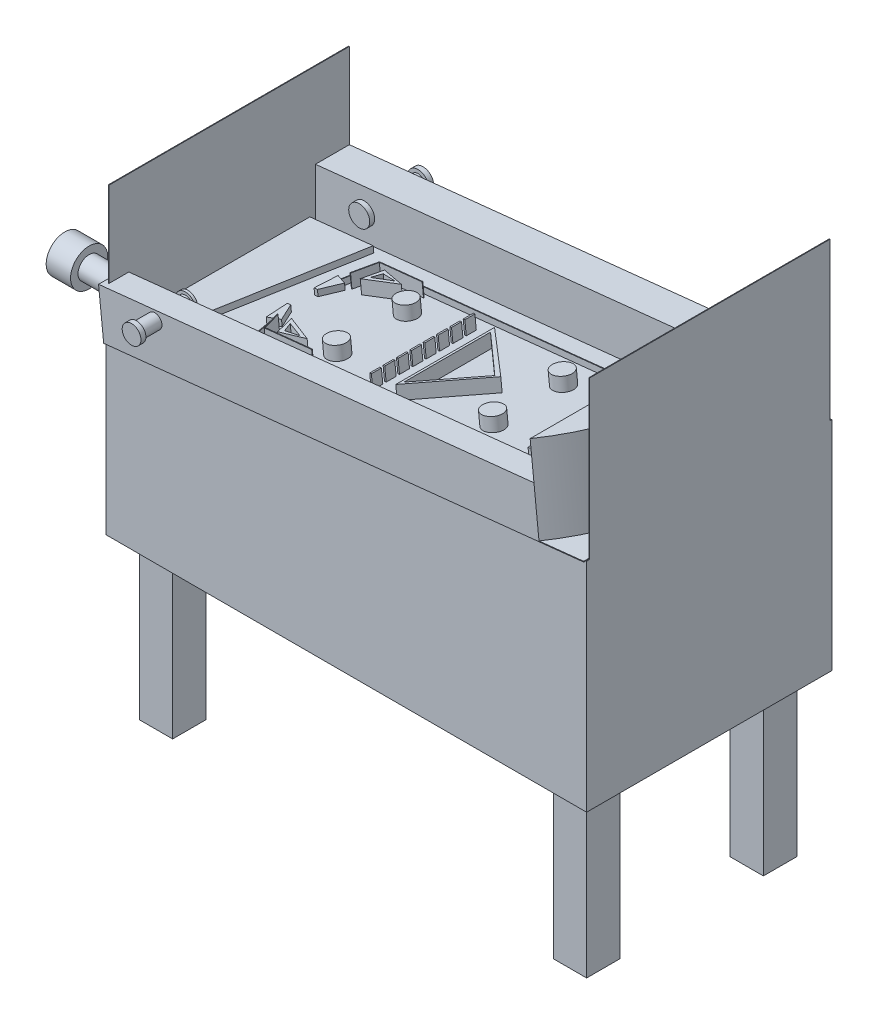
SolidWorks part; units mm, degrees
ref_plane "Front Plane" through (0, 0, 0) normal (0, 0, 1) x (1, 0, 0)
ref_plane "Top Plane" through (0, 0, 0) normal (0, 1, 0) x (1, 0, 0)
ref_plane "Right Plane" through (0, 0, 0) normal (1, 0, 0) x (0, 0, -1)
sketch "Sketch1" plane through (0, 0, 0) normal (0, 1, 0) x (1, 0, 0)
  line L1 (914.4, -457.2) -> (-914.4, -457.2)
  line L2 (914.4, -457.2) -> (914.4, 457.2)
  line L3 (914.4, 457.2) -> (-914.4, 457.2)
  line L4 (-914.4, -457.2) -> (-914.4, 457.2)
  line L5 (914.4, -457.2) -> (-914.4, 457.2) construction
  line L6 (914.4, 457.2) -> (-914.4, -457.2) construction
  point P0 (0, 0)
  dimension "D1" = 914.4
  dimension "D2" = 1828.8
extrude "Boss-Extrude1" add sketch "Sketch1" along normal blind 2.54
sketch "Sketch2" plane through (0, 2.54, 0) normal (0, 1, 0) x (1, 0, 0)
  line L0 (-914.4, 457.2) -> (-914.4, -457.2)
  line L1 (914.4, 457.2) -> (-914.4, 457.2) construction
  line L2 (-914.4, 457.2) -> (-914.4, -457.2) construction
  line L3 (-914.4, -457.2) -> (914.4, -457.2) construction
sketch "Sketch3" plane through (0, 2.54, 0) normal (0, 1, 0) x (1, 0, 0)
  line L0 (914.4, 457.2) -> (914.4, -457.2)
  line L1 (914.4, 457.2) -> (-914.4, 457.2) construction
  line L2 (914.4, -457.2) -> (914.4, 457.2) construction
extrude "Extrude-Thin8" add sketch "Sketch2" along normal blind 1143 separate body thin
extrude "Extrude-Thin9" add sketch "Sketch3" along normal blind 1422.4 thin
sketch "Sketch15" plane through (-914.4, 0, 0) normal (1, 0, 0) x (0, 0, -1)
  line L0 (-457.2, 1145.54) -> (457.2, 1145.54)
  line L1 (457.2, 1145.54) -> (-457.2, 1145.54) construction
  line L2 (457.2, 1145.54) -> (457.2, 2.54) construction
  line L3 (-457.2, 637.54) -> (457.2, 637.54) construction
  line L4 (-457.2, 1145.54) -> (-457.2, 2.54) construction
  line L5 (457.2, 2.54) -> (-457.2, 2.54) construction
  point P11 (0, 637.54)
  point P14 (0, 2.54)
  dimension "D1" = 635
sketch "Sketch17" plane through (911.86, 0, 0) normal (-1, 0, 0) x (0, 0, 1)
  line L0 (-457.2, 1424.94) -> (457.2, 1424.94)
  line L1 (-457.2, 829.7545) -> (477.8068, 829.7545) construction
  line L2 (-457.2, 1424.94) -> (-457.2, 2.54) construction
  line L3 (-457.2, 2.54) -> (457.2, 2.54) construction
  dimension "D1" = 827.2145
ref_plane "Plane3" through (-76.3845, 725.7414, 0) normal (0.1047, -0.9945, 0) x (-0.9945, -0.1047, 0)
sketch "Sketch18" plane through (-76.3845, 725.7414, 0) normal (0.1047, -0.9945, 0) x (-0.9945, -0.1047, 0)
  line L1 (842.6443, 457.2) -> (-993.7032, 457.2)
  line L2 (842.6443, 457.2) -> (842.6443, -477.8068)
  line L3 (842.6443, -477.8068) -> (-993.7032, -477.8068)
  line L4 (-993.7032, 457.2) -> (-993.7032, -477.8068)
extrude "Boss-Extrude3" add sketch "Sketch18" along normal blind 2.54
ref_plane "Plane4" through (-192.1612, 1256.0355, 0) normal (0.1512, -0.9885, 0) x (-0.9885, -0.1512, 0)
sketch "Sketch20" plane through (-76.3845, 725.7414, 0) normal (-0.1047, 0.9945, 0) x (0.9945, 0.1047, 0)
  line L0 (993.7032, 457.2) -> (-842.6443, 457.2)
sketch "Sketch22" plane through (911.86, 0, 0) normal (-1, 0, 0) x (0, 0, 1)
  line L0 (-457.2, 1424.94) -> (-457.2, 829.7545)
sketch "Sketch23" plane through (-914.4, 0, 0) normal (1, 0, 0) x (0, 0, -1)
  line L0 (457.2, 1145.54) -> (457.2, 637.54)
ref_plane "Plane5" through (0, 0, -457.2) normal (0, 0, -1) x (-1, 0, 0)
sketch "Sketch24" plane through (0, 0, -457.2) normal (0, 0, -1) x (-1, 0, 0)
  line L0 (916.94, 1145.54) -> (914.4, 637.54)
  line L1 (914.4, 637.54) -> (-911.86, 827.2005)
  line L2 (-911.86, 827.2005) -> (-911.86, 1424.94)
  line L3 (-911.86, 1424.94) -> (916.94, 1145.54)
sketch "Sketch25" plane through (0, 0, -457.2) normal (0, 0, -1) x (-1, 0, 0)
  line L0 (-914.4, 0) -> (914.4, 0)
  line L1 (914.4, 0) -> (914.1341, 635.014)
sketch "Sketch26" plane through (0, 0, 0) normal (0, 0, 1) x (1, 0, 0)
  line L1 (911.86, 829.7545) -> (-914.4, 637.54) construction
  line L2 (914.4, 0) -> (-914.4, 0) construction
  line L3 (914.4, 0) -> (-914.4, 0)
  line L4 (-914.4, 0) -> (-914.4, 637.54)
  line L5 (-916.94, 1145.54) -> (-914.4, 637.54) construction
  line L7 (-914.4, 637.54) -> (914.4, 827.2145)
  line L8 (914.4, 827.2145) -> (914.4, 0)
  dimension "D1" = 914.4
  dimension "D2" = 827.2145
  dimension "D3" = 1828.8
extrude "Boss-Extrude8" add sketch "Sketch26" along normal blind 469.138 and the other way blind 463.804
sketch "Sketch29" plane through (0, 0, 0) normal (0, -1, 0) x (1, 0, 0)
  line L0 (-787.4, 469.138) -> (-787.4, -457.4404) construction
  line L1 (-914.4, 469.138) -> (914.4, 469.138) construction
  line L3 (787.5718, 469.138) -> (787.5718, -457.2) construction
  line L4 (914.4, -457.2) -> (-914.4, -457.2) construction
  line L5 (-914.4, -330.2) -> (787.5718, -330.2) construction
  line L6 (-914.4, -463.804) -> (-914.4, 469.138) construction
  line L7 (-914.4, 342.138) -> (787.5718, 342.138) construction
  line L9 (-723.9, 278.638) -> (-850.9, 278.638)
  line L10 (-723.9, 278.638) -> (-723.9, 405.638)
  line L11 (-723.9, 405.638) -> (-850.9, 405.638)
  line L12 (-850.9, 278.638) -> (-850.9, 405.638)
  line L13 (-723.9, 278.638) -> (-850.9, 405.638) construction
  line L14 (-723.9, 405.638) -> (-850.9, 278.638) construction
  line L15 (-850.9, -393.7) -> (-723.9, -393.7)
  line L16 (-850.9, -393.7) -> (-850.9, -266.7)
  line L17 (-850.9, -266.7) -> (-723.9, -266.7)
  line L18 (-723.9, -393.7) -> (-723.9, -266.7)
  line L19 (-850.9, -393.7) -> (-723.9, -266.7) construction
  line L20 (-850.9, -266.7) -> (-723.9, -393.7) construction
  line L21 (851.0718, -393.7) -> (724.0718, -393.7)
  line L22 (851.0718, -393.7) -> (851.0718, -266.7)
  line L23 (851.0718, -266.7) -> (724.0718, -266.7)
  line L24 (724.0718, -393.7) -> (724.0718, -266.7)
  line L25 (851.0718, -393.7) -> (724.0718, -266.7) construction
  line L26 (851.0718, -266.7) -> (724.0718, -393.7) construction
  line L27 (851.0718, 405.638) -> (724.0718, 405.638)
  line L28 (851.0718, 405.638) -> (851.0718, 278.638)
  line L29 (851.0718, 278.638) -> (724.0718, 278.638)
  line L30 (724.0718, 405.638) -> (724.0718, 278.638)
  line L31 (851.0718, 405.638) -> (724.0718, 278.638) construction
  line L32 (851.0718, 278.638) -> (724.0718, 405.638) construction
  point P16 (-787.4, 342.138)
  point P21 (-787.4, -330.2)
  dimension "D1" = 127
  dimension "D2" = 127
  dimension "D3" = 127
  dimension "D4" = 127
  dimension "D5" = 127
  dimension "D6" = 127
  dimension "D7" = 127
  dimension "D8" = 127
  dimension "D9" = 127
  dimension "D10" = 127
  dimension "D11" = 127
  dimension "D12" = 127
extrude "Boss-Extrude9" add sketch "Sketch29" along normal blind 609.6
sketch "Sketch30" plane through (-76.3845, 725.7414, 0) normal (-0.1047, 0.9945, 0) x (0.9945, 0.1047, 0)
  line L0 (993.7032, 457.2) -> (993.7032, -477.8068)
  line L1 (993.7032, 457.2) -> (822.8717, 457.2)
  line L2 (993.7032, -477.8068) -> (822.8717, -477.8068)
  line L3 (822.8717, 457.2) -> (822.8717, -477.8068)
extrude "Boss-Extrude10" add sketch "Sketch30" along normal blind 322.072
sketch "Sketch32" plane through (-110.0965, 1046.0442, 0) normal (-0.1047, 0.9945, 0) x (0.9945, 0.1047, 0)
  arc A0 (822.8717, 457.2) -> (822.8717, -477.8068) centre (268.5944, -10.3034) cw
extrude "Cut-Extrude1" cut sketch "Sketch32" against normal blind 322.072 and the other way through all
sketch "Sketch34" plane through (-76.3845, 725.7414, 0) normal (-0.1047, 0.9945, 0) x (0.9945, 0.1047, 0)
  line L0 (-842.6443, -477.8068) -> (822.8717, -477.8068)
  line L1 (-842.6443, -477.8068) -> (-842.6443, -381.7986)
  line L2 (822.8717, -477.8068) -> (822.8717, -381.7986)
  line L3 (-842.6443, -381.7986) -> (822.8717, -381.7986)
extrude "Boss-Extrude12" add sketch "Sketch34" along normal blind 183.134
sketch "Sketch35" plane through (-76.3845, 725.7414, 0) normal (-0.1047, 0.9945, 0) x (0.9945, 0.1047, 0)
  line L0 (822.8717, 457.2) -> (-842.6443, 457.2)
  line L1 (822.8717, 457.2) -> (822.8717, 328.2193)
  line L2 (-842.6443, 457.2) -> (-842.6443, 328.2193)
  line L3 (822.8717, 328.2193) -> (-842.6443, 328.2193)
sketch "Sketch36" plane through (-76.3845, 725.7414, 0) normal (-0.1047, 0.9945, 0) x (0.9945, 0.1047, 0)
  line L0 (604.8922, -283.7239) -> (-596.2814, -283.7239)
  line L1 (604.8922, -283.7239) -> (604.8922, -229.3315)
  line L2 (604.8922, -229.3315) -> (-596.2814, -229.3315)
  line L3 (-596.2814, -229.3315) -> (-596.2814, -283.7239)
extrude "Boss-Extrude14" add sketch "Sketch36" along normal blind 22.86
extrude "Boss-Extrude16" add sketch "Sketch35" along normal blind 183.134
sketch "Sketch38" plane through (-76.3845, 725.7414, 0) normal (-0.1047, 0.9945, 0) x (0.9945, 0.1047, 0)
  line L0 (-596.2814, -283.7239) -> (-838.4892, -283.7239) construction
  line L1 (-838.4892, -283.7239) -> (-717.3853, -283.7239)
  line L2 (-717.3853, -283.7239) -> (-596.2814, 305.143)
  line L3 (-596.2814, 305.143) -> (-838.4892, 305.143)
  line L4 (-838.4892, 305.143) -> (-838.4892, -283.7239)
  dimension "D1" = 0
extrude "Boss-Extrude18" add sketch "Sketch38" along normal blind 22.86
sketch "Sketch40" plane through (-76.3845, 725.7414, 0) normal (-0.1047, 0.9945, 0) x (0.9945, 0.1047, 0)
  line L0 (-842.6443, -381.7986) -> (-842.6443, -285.5515) construction
  line L1 (822.8717, -381.7986) -> (-842.6443, -381.7986) construction
  line L2 (-842.6443, 328.2193) -> (-842.6443, -381.7986) construction
sketch "Sketch41" plane through (-914.4, 0, 0) normal (1, 0, 0) x (0, 0, -1)
  line L0 (-329.7438, 633.9885) -> (-329.7438, 1141.9885) construction
  line L1 (328.2193, 637.54) -> (328.2193, 821.6856) construction
  dimension "D1" = 657.9631
sketch "Sketch42" plane through (-914.4, 0, 0) normal (1, 0, 0) x (0, 0, -1)
  circle A0 centre (-327.0284, 706.3908) radius 42.4066
extrude "Boss-Extrude19" add sketch "Sketch42" against normal blind 211.074 and the other way blind 243.078
sketch "Sketch43" plane through (-1125.474, 0, 0) normal (-1, 0, 0) x (0, 0, 1)
  circle A0 centre (327.0284, 706.3908) radius 69.1347
extrude "Cut-Extrude3" cut sketch "Sketch43" along normal blind 92.71 and the other way blind 5.334
sketch "Sketch45" plane through (-1120.14, 0, 0) normal (-1, 0, 0) x (0, 0, 1)
  circle A0 centre (327.0284, 706.3908) radius 70.7844
extrude "Boss-Extrude20" add sketch "Sketch45" along normal blind 92.71
sketch "Sketch47" plane through (-78.7773, 748.4758, 0) normal (-0.1047, 0.9945, 0) x (0.9945, 0.1047, 0)
  line L0 (-596.2814, -229.3315) -> (-596.2814, -283.7239) construction
  point P0 (-596.2814, -256.5277)
sketch "Sketch48" plane through (-78.7773, 748.4758, 0) normal (-0.1047, 0.9945, 0) x (0.9945, 0.1047, 0)
  line L0 (-717.3853, -283.7239) -> (-596.2814, 305.143) construction
  point P0 (-711.7922, -256.5277)
sketch "Sketch52" plane through (-76.3845, 725.7414, 0) normal (-0.1047, 0.9945, 0) x (0.9945, 0.1047, 0)
  line L0 (615.085, -255.0187) -> (822.8717, -255.0187) construction
  line L1 (822.8717, 328.2193) -> (822.8717, -381.7986) construction
  line L2 (615.085, -294.4706) -> (615.085, -381.7986) construction
  line L3 (822.8717, -381.7986) -> (-842.6443, -381.7986) construction
  dimension "D1" = 207.7867
  dimension "D2" = 126.7799
sketch "Sketch53" plane through (-76.3845, 725.7414, 0) normal (-0.1047, 0.9945, 0) x (0.9945, 0.1047, 0)
  line L0 (-842.6443, 328.2193) -> (822.8717, 328.2193) construction
  arc A0 (615.085, -359.6876) -> (615.085, 328.2193) centre (431.9409, -15.7341) ccw
  point P0 (658.265, -256.9804)
  dimension "D1" = 43.18
extrude "Extrude-Thin12" add sketch "Sketch53" along normal blind 137.16 thin
sketch "Sketch57" plane through (-76.3845, 725.7414, 0) normal (-0.1047, 0.9945, 0) x (0.9945, 0.1047, 0)
  arc A0 (614.4555, -363.1309) -> (568.9484, -379.2389) centre (578.0916, -332.734) cw
extrude "Extrude-Thin17" add sketch "Sketch57" along normal blind 137.16 thin
sketch "Sketch58" plane through (0, 0, -457.2) normal (0, 0, -1) x (-1, 0, 0)
  circle A0 centre (720.9732, 762.1711) radius 27.1239
extrude "Boss-Extrude21" add sketch "Sketch58" along normal blind 67.818 and the other way blind 137.16
sketch "Sketch59" plane through (0, 0, -320.04) normal (0, 0, 1) x (1, 0, 0)
  circle A0 centre (-720.9732, 762.1711) radius 39.9415
extrude "Boss-Extrude22" add sketch "Sketch59" along normal blind 18.796
sketch "Sketch60" plane through (0, 0, -525.018) normal (0, 0, -1) x (-1, 0, 0)
  circle A0 centre (720.9732, 762.1711) radius 40.5842
extrude "Boss-Extrude23" add sketch "Sketch60" along normal blind 18.796
sketch "Sketch62" plane through (0, 0, 477.8068) normal (0, 0, 1) x (1, 0, 0)
  line L0 (-923.8516, 727.341) -> (-719.5701, 748.8417) construction
  line L1 (-914.1341, 635.014) -> (-933.569, 819.668) construction
sketch "Sketch63" plane through (0, 0, 477.8068) normal (0, 0, 1) x (1, 0, 0)
  circle A0 centre (-719.5701, 748.8417) radius 27.1018
sketch "Sketch64" plane through (0, 0, 477.8068) normal (0, 0, 1) x (1, 0, 0)
  line L0 (-719.5701, 805.7131) -> (-929.7717, 783.5893) construction
  line L1 (-914.1341, 635.014) -> (-933.569, 819.668) construction
  circle A0 centre (-719.5701, 805.7131) radius 27.178
  dimension "D1" = 56.8714
extrude "Boss-Extrude25" add sketch "Sketch64" along normal blind 69.596 and the other way blind 116.332
sketch "Sketch65" plane through (0, 0, 361.4748) normal (0, 0, -1) x (-1, 0, 0)
  circle A0 centre (719.5701, 805.7131) radius 37.6452
sketch "Sketch66" plane through (0, 0, 547.4028) normal (0, 0, 1) x (1, 0, 0)
  circle A0 centre (-719.5701, 805.7131) radius 35.7405
extrude "Boss-Extrude27" add sketch "Sketch66" along normal blind 18.796
sketch "Sketch68" plane through (-76.3845, 725.7414, 0) normal (-0.1047, 0.9945, 0) x (0.9945, 0.1047, 0)
  line L0 (-240.8124, 328.2193) -> (-240.8124, 238.8535) construction
  line L1 (-842.6443, 328.2193) -> (615.085, 328.2193) construction
  line L2 (-240.8124, 238.8535) -> (616.9031, 238.8535)
  line L3 (-240.8124, 238.8535) -> (-519.1537, 238.8535)
  line L4 (-717.3853, -283.7239) -> (-596.2814, 305.143) construction
  line L5 (-519.1537, 238.8535) -> (-541.3694, 121.5588)
  line L6 (546.6472, 0) -> (-546.6472, 0) construction
  line L7 (-240.8124, -238.8535) -> (616.9031, -238.8535)
  line L8 (-240.8124, -238.8535) -> (-519.1537, -238.8535)
  line L9 (-519.1537, -238.8535) -> (-541.3694, -121.5588)
  point P13 (0, 0)
  dimension "D1" = 88.9
  dimension "D2" = 119.38
sketch "Sketch70" plane through (-76.3845, 725.7414, 0) normal (-0.1047, 0.9945, 0) x (0.9945, 0.1047, 0)
  line L0 (-561.1432, 136.6047) -> (-519.5262, 119.842)
  line L1 (-561.1432, 136.6047) -> (-566.7099, 50.8)
  line L2 (-566.7099, 50.8) -> (-553.7046, 50.8)
  line L3 (-553.7046, 50.8) -> (-519.5262, 119.842)
  line L4 (566.7099, 0) -> (-566.7099, 0) construction
  line L5 (-566.7099, -50.8) -> (-553.7046, -50.8)
  line L6 (-553.7046, -50.8) -> (-519.5262, -119.842)
  line L7 (-561.1432, -136.6047) -> (-519.5262, -119.842)
  line L8 (-561.1432, -136.6047) -> (-566.7099, -50.8)
  point P10 (0, 0)
  dimension "D1" = 13.0053
  dimension "D2" = 101.6
extrude "Extrude-Thin23" add sketch "Sketch68" along normal blind 22.86 thin thin type one direction wall 2.54
extrude "Boss-Extrude30" add sketch "Sketch70" along normal blind 22.86
extrude "Boss-Extrude31" add sketch "Sketch65" along normal blind 10.16
sketch "Sketch71" plane through (-76.3845, 725.7414, 0) normal (-0.1047, 0.9945, 0) x (0.9945, 0.1047, 0)
  line L0 (540.6362, 238.8535) -> (540.6362, -229.3315) construction
  line L1 (616.9031, 238.8535) -> (-519.1537, 238.8535) construction
  line L2 (604.8922, -229.3315) -> (-518.372, -229.3315) construction
  line L4 (566.0362, 127.0935) -> (515.2362, 127.0935)
  line L5 (566.0362, 127.0935) -> (566.0362, 147.4135)
  line L6 (566.0362, 147.4135) -> (515.2362, 147.4135)
  line L7 (515.2362, 127.0935) -> (515.2362, 147.4135)
  line L8 (566.0362, 127.0935) -> (515.2362, 147.4135) construction
  line L9 (566.0362, 147.4135) -> (515.2362, 127.0935) construction
  line L10 (566.0362, 15.3335) -> (515.2362, 15.3335)
  line L11 (566.0362, 15.3335) -> (566.0362, 35.6535)
  line L12 (566.0362, 35.6535) -> (515.2362, 35.6535)
  line L13 (515.2362, 15.3335) -> (515.2362, 35.6535)
  line L14 (566.0362, 15.3335) -> (515.2362, 35.6535) construction
  line L15 (566.0362, 35.6535) -> (515.2362, 15.3335) construction
  line L16 (566.0362, -96.4265) -> (515.2362, -96.4265)
  line L17 (566.0362, -96.4265) -> (566.0362, -76.1065)
  line L18 (566.0362, -76.1065) -> (515.2362, -76.1065)
  line L19 (515.2362, -96.4265) -> (515.2362, -76.1065)
  line L20 (566.0362, -96.4265) -> (515.2362, -76.1065) construction
  line L21 (566.0362, -76.1065) -> (515.2362, -96.4265) construction
  line L22 (566.0362, -208.1865) -> (515.2362, -208.1865)
  line L23 (566.0362, -208.1865) -> (566.0362, -187.8665)
  line L24 (566.0362, -187.8665) -> (515.2362, -187.8665)
  line L25 (515.2362, -208.1865) -> (515.2362, -187.8665)
  line L26 (566.0362, -208.1865) -> (515.2362, -187.8665) construction
  line L27 (566.0362, -187.8665) -> (515.2362, -208.1865) construction
  point P6 (540.6362, 137.2535)
  point P7 (540.6362, -127.7315)
  point P8 (540.6362, 137.2535)
  point P13 (540.6362, 127.0935)
  point P14 (540.6362, 25.4935)
  point P15 (540.6362, 25.4935)
  point P20 (540.6362, 15.3335)
  point P21 (540.6362, -86.2665)
  point P22 (540.6362, -86.2665)
  point P27 (540.6362, -96.4265)
  point P28 (540.6362, -198.0265)
  point P29 (540.6362, -198.0265)
  point P34 (540.6362, -208.1865)
  point P36 (540.6362, -229.3315)
  dimension "D1" = 101.6
  dimension "D2" = 101.6
  dimension "D3" = 101.6
  dimension "D4" = 20.32
  dimension "D5" = 50.8
  dimension "D6" = 20.32
  dimension "D7" = 50.8
  dimension "D8" = 101.6
  dimension "D9" = 20.32
  dimension "D10" = 50.8
  dimension "D11" = 101.6
  dimension "D12" = 20.32
extrude "Boss-Extrude33" add sketch "Sketch71" along normal blind 50.8
sketch "Sketch73" plane through (-76.3845, 725.7414, 0) normal (-0.1047, 0.9945, 0) x (0.9945, 0.1047, 0)
  circle A0 centre (477.1849, 80.7647) radius 25.4 construction
  circle A1 centre (477.1849, -38.7712) radius 25.4 construction
  circle A2 centre (477.1849, -144.0597) radius 25.4 construction
sketch "Sketch74" plane through (-76.3845, 725.7414, 0) normal (-0.1047, 0.9945, 0) x (0.9945, 0.1047, 0)
  line L0 (-511.587, 135.8769) -> (-488.9935, 225.4742)
  line L1 (-488.9935, 225.4742) -> (-323.4538, 225.4742)
  line L2 (-511.587, -138.1364) -> (-488.9935, -208.8189)
  line L3 (-488.9935, -208.8189) -> (-309.2899, -208.8189)
  point P5 (0, 0)
  point P7 (-488.9935, -208.8189)
  point P8 (-511.587, 135.8769)
  point P9 (-511.587, -138.1364)
extrude "Extrude-Thin24" add sketch "Sketch74" along normal blind 50.8 thin
sketch "Sketch76" plane through (-76.3845, 725.7414, 0) normal (-0.1047, 0.9945, 0) x (0.9945, 0.1047, 0)
  line L0 (-467.4514, 130.6852) -> (-359.0649, 179.1739)
  line L1 (-359.0649, 179.1739) -> (-447.6391, 203.3305)
  line L2 (-447.6391, 203.3305) -> (-467.4514, 130.6852)
  line L3 (511.6617, 0) -> (-511.6617, 0) construction
  line L4 (-359.0649, -179.1739) -> (-447.6391, -203.3305)
  line L5 (-467.4514, -130.6852) -> (-359.0649, -179.1739)
  line L6 (-447.6391, -203.3305) -> (-467.4514, -130.6852)
  point P8 (0, 0)
extrude "Boss-Extrude34" add sketch "Sketch76" along normal blind 50.8
sketch "Sketch78" plane through (-76.3845, 725.7414, 0) normal (-0.1047, 0.9945, 0) x (0.9945, 0.1047, 0)
  line L0 (-436.6852, 187.6275) -> (-450.8896, 152.1166)
  line L1 (-450.8896, 152.1166) -> (-384.3169, 180.6478)
  line L2 (-384.3169, 180.6478) -> (-436.6852, 187.6275)
  line L3 (506.8145, 0) -> (-506.8145, 0) construction
  line L4 (-450.8896, -152.1166) -> (-384.3169, -180.6478)
  line L5 (-384.3169, -180.6478) -> (-436.6852, -187.6275)
  line L6 (-436.6852, -187.6275) -> (-450.8896, -152.1166)
  point P2 (-384.3169, -180.6478)
  point P7 (0, 0)
  point P9 (-450.8896, -152.1166)
extrude "Cut-Extrude5" cut sketch "Sketch78" against normal blind 50.8 and the other way blind 50.8
sketch "Sketch79" plane through (-76.3845, 725.7414, 0) normal (-0.1047, 0.9945, 0) x (0.9945, 0.1047, 0)
  line L0 (-298.6727, 238.8535) -> (-298.6727, -229.3315) construction
  line L1 (616.9031, 238.8535) -> (-519.1537, 238.8535) construction
  line L2 (604.8922, -229.3315) -> (-518.372, -229.3315) construction
  line L3 (604.8922, -229.3315) -> (-518.372, -229.3315) construction
  line L4 (0, -221.3652) -> (0, 221.3652) construction
  line L5 (298.6727, 238.8535) -> (298.6727, -229.3315) construction
  circle A0 centre (-298.6727, 137.2535) radius 38.1
  circle A1 centre (-298.6727, -127.7315) radius 38.1
  circle A2 centre (298.6727, 137.2535) radius 38.1
  circle A3 centre (298.6727, -127.7315) radius 38.1
  point P6 (-298.6727, 137.2535)
  point P9 (-298.6727, -127.7315)
  point P10 (-298.6727, 238.8535)
  point P15 (0, 0)
  point P18 (371.3378, 167.844)
  point P19 (371.3378, -158.322)
  dimension "D1" = 101.6
  dimension "D2" = 101.6
  dimension "D3" = 101.6
  dimension "D4" = 101.6
extrude "Boss-Extrude35" add sketch "Sketch79" along normal blind 50.8
sketch "Sketch80" plane through (-76.3845, 725.7414, 0) normal (-0.1047, 0.9945, 0) x (0.9945, 0.1047, 0)
  line L0 (0, 176.8518) -> (0, -199.0655) construction
  line L1 (195.7007, 5.887) -> (0, 176.8518)
  line L2 (195.7007, 5.887) -> (0, -199.0655)
  line L3 (0, 176.8518) -> (0, -199.0655)
extrude "Boss-Extrude36" add sketch "Sketch80" along normal blind 50.8
sketch "Sketch81" plane through (-81.7019, 776.2624, 0) normal (-0.1047, 0.9945, 0) x (0.9945, 0.1047, 0)
  line L0 (8.9563, 152.5216) -> (8.9563, -176.651)
  line L1 (8.9563, -176.651) -> (178.8211, 0)
  line L2 (178.8211, 0) -> (8.9563, 152.5216)
extrude "Cut-Extrude6" cut sketch "Sketch81" against normal blind 50.8
sketch "Sketch82" plane through (-76.3845, 725.7414, 0) normal (-0.1047, 0.9945, 0) x (0.9945, 0.1047, 0)
  line L0 (-94.9488, 182.5211) -> (-94.9488, -157.9671) construction
  line L1 (0, 176.8518) -> (0, -199.0655) construction
  line L2 (-98.1143, 104.3701) -> (-98.1143, 142.4701)
  line L3 (-91.7833, 155.1701) -> (-98.1143, 155.1701)
  line L4 (-91.7833, 155.1701) -> (-91.7833, 193.2701)
  line L5 (-91.7833, 193.2701) -> (-98.1143, 193.2701)
  line L6 (-98.1143, 155.1701) -> (-98.1143, 193.2701)
  line L7 (-91.7833, 155.1701) -> (-98.1143, 193.2701) construction
  line L8 (-91.7833, 193.2701) -> (-98.1143, 155.1701) construction
  line L9 (-91.7833, 104.3701) -> (-98.1143, 104.3701)
  line L10 (-91.7833, 104.3701) -> (-91.7833, 142.4701)
  line L11 (-91.7833, 142.4701) -> (-98.1143, 142.4701)
  line L12 (-98.1143, 53.5701) -> (-98.1143, 91.6701)
  line L13 (-91.7833, 53.5701) -> (-98.1143, 53.5701)
  line L14 (-91.7833, 53.5701) -> (-91.7833, 91.6701)
  line L15 (-91.7833, 91.6701) -> (-98.1143, 91.6701)
  line L16 (-98.1143, 2.7701) -> (-98.1143, 40.8701)
  line L17 (-91.7833, 2.7701) -> (-98.1143, 2.7701)
  line L18 (-91.7833, 2.7701) -> (-91.7833, 40.8701)
  line L19 (-91.7833, 40.8701) -> (-98.1143, 40.8701)
  line L20 (-98.1143, -48.0299) -> (-98.1143, -9.9299)
  line L21 (-91.7833, -48.0299) -> (-98.1143, -48.0299)
  line L22 (-91.7833, -48.0299) -> (-91.7833, -9.9299)
  line L23 (-91.7833, -9.9299) -> (-98.1143, -9.9299)
  line L24 (-98.1143, -98.8299) -> (-98.1143, -60.7299)
  line L25 (-91.7833, -98.8299) -> (-98.1143, -98.8299)
  line L26 (-91.7833, -98.8299) -> (-91.7833, -60.7299)
  line L27 (-91.7833, -60.7299) -> (-98.1143, -60.7299)
  line L28 (-98.1143, -149.6299) -> (-98.1143, -111.5299)
  line L29 (-91.7833, -149.6299) -> (-98.1143, -149.6299)
  line L30 (-91.7833, -149.6299) -> (-91.7833, -111.5299)
  line L31 (-91.7833, -111.5299) -> (-98.1143, -111.5299)
  line L32 (-98.1143, -200.4299) -> (-98.1143, -162.3299)
  line L33 (-91.7833, -200.4299) -> (-98.1143, -200.4299)
  line L34 (-91.7833, -200.4299) -> (-91.7833, -162.3299)
  line L35 (-91.7833, -162.3299) -> (-98.1143, -162.3299)
  point P4 (-94.9488, 174.2201)
  dimension "D1" = 38.1
  dimension "D2" = 8
extrude "Boss-Extrude37" add sketch "Sketch82" along normal blind 50.8
